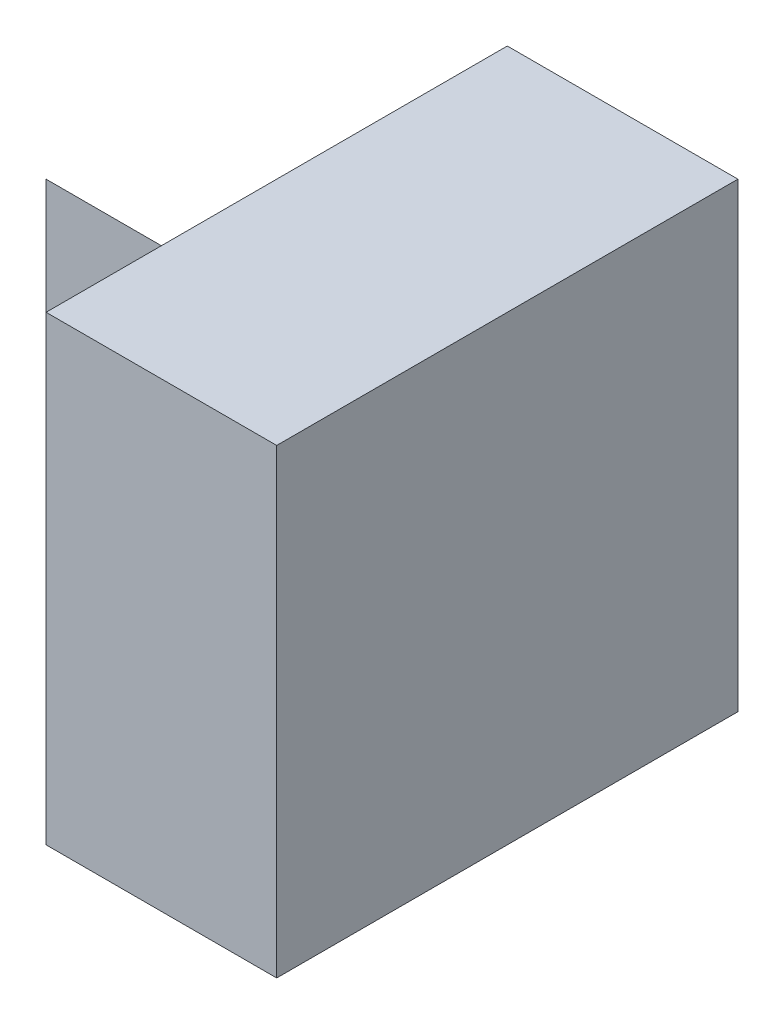
SolidWorks part; units mm, degrees
ref_plane "Front Plane" through (0, 0, 0) normal (0, 0, 1) x (1, 0, 0)
ref_plane "Top Plane" through (0, 0, 0) normal (0, 1, 0) x (1, 0, 0)
ref_plane "Right Plane" through (0, 0, 0) normal (1, 0, 0) x (0, 0, -1)
sketch "Sketch1" plane through (0, 0, 0) normal (1, 0, 0) x (0, 0, -1)
  line L1 (0, 0) -> (4, 0)
  line L2 (0, 0) -> (0, 4)
  line L3 (0, 4) -> (4, 4)
  line L4 (4, 0) -> (4, 4)
  dimension "D1" = 4
  dimension "D2" = 4
extrude "Boss-Extrude1" add sketch "Sketch1" along normal blind 2
sketch "Sketch2" plane through (0, 0, 0) normal (-1, 0, 0) x (0, 0, 1)
  line L1 (-4, 0) -> (-2, 0)
  line L2 (-4, 0) -> (-4, 3)
  line L3 (-4, 3) -> (-2, 3)
  line L4 (-2, 0) -> (-2, 3)
  dimension "D1" = 3
  dimension "D2" = 2
extrude "Boss-Extrude2" add sketch "Sketch2" along normal blind 2
sketch "Sketch3" plane through (-2, 0, 0) normal (-1, 0, 0) x (0, 0, 1)
  line L0 (-2, 3) -> (-4, 0)
  line L1 (-4, 0) -> (-2, 0)
  line L2 (-2, 0) -> (-2, 3)
  line M4 (-4, 3) -> (-4, 0)
  line M7 (-2, 3) -> (-4, 3)
extrude "Cut-Extrude1" cut sketch "Sketch3" against normal blind 2 contours L0 M7 M4
